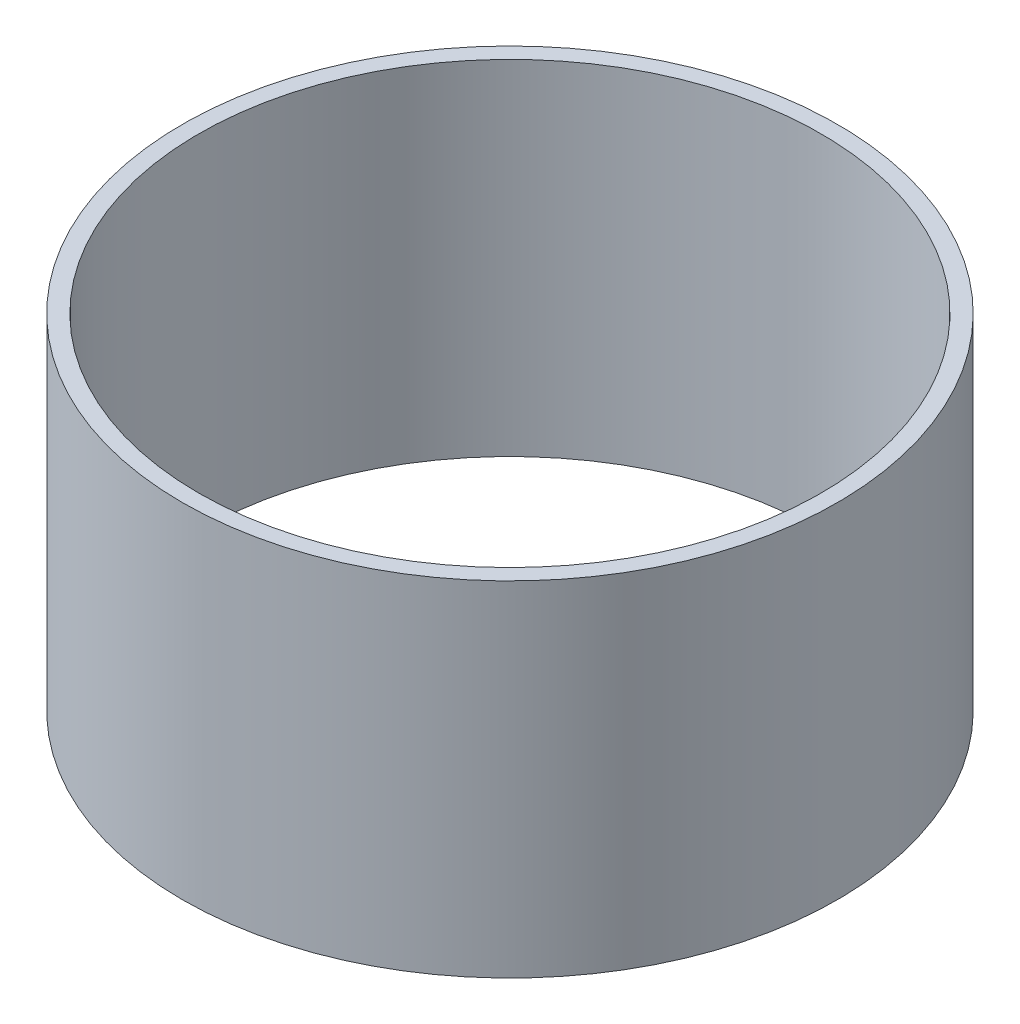
SolidWorks part; units mm, degrees
material "1060 合金"
ref_plane "前视基准面" through (0, 0, 0) normal (0, 0, 1) x (1, 0, 0)
ref_plane "上视基准面" through (0, 0, 0) normal (0, 1, 0) x (1, 0, 0)
ref_plane "右视基准面" through (0, 0, 0) normal (1, 0, 0) x (0, 0, -1)
other "Configuration Table"
sketch "草图1" plane through (0, 0, 0) normal (0, 1, 0) x (1, 0, 0)
  circle A0 centre (0, 0) radius 40
  circle A1 centre (0, 0) radius 38
extrude "凸台-拉伸1" add sketch "草图1" along normal blind 42
